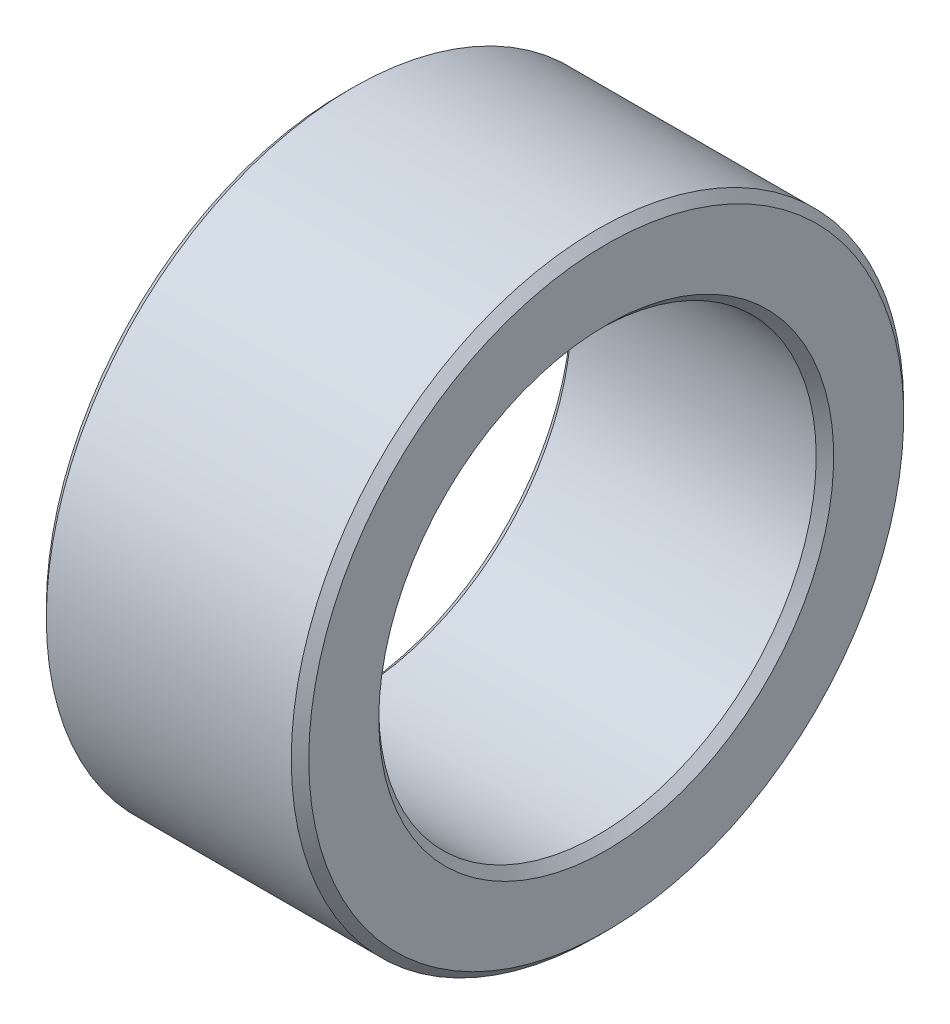
SolidWorks part; units mm, degrees
material "Простая углеродистая сталь"
ref_plane "Спереди  XY" through (0, 0, 0) normal (0, 0, 1) x (1, 0, 0)
ref_plane "Сверху  XZ" through (0, 0, 0) normal (0, 1, 0) x (1, 0, 0)
ref_plane "Справа  ZY" through (0, 0, 0) normal (1, 0, 0) x (0, 0, -1)
sketch "Эскиз1" plane through (0, 0, 0) normal (0, 0, 1) x (1, 0, 0)
  line L0 (0, 0) -> (6, 0) construction
  line L1 (0.2, 5) -> (5.8, 5)
  line L2 (6, 5.2) -> (6, 6.8)
  line L3 (5.8, 7) -> (0.2, 7)
  line L4 (0, 6.8) -> (0, 5.2)
  line L5 (0, 5.2) -> (0.2, 5)
  line L6 (0.2, 7) -> (0, 6.8)
  line L7 (6, 6.8) -> (5.8, 7)
  line L8 (5.8, 5) -> (6, 5.2)
  point P3 (0, 5)
  point P4 (6, 5)
  point P6 (6, 7)
  point P7 (0, 7)
  dimension "D1" = 6
  dimension "D2" = 5
  dimension "D3" = 7
revolve "Повернуть1" add sketch "Эскиз1" angle 360 about L0
